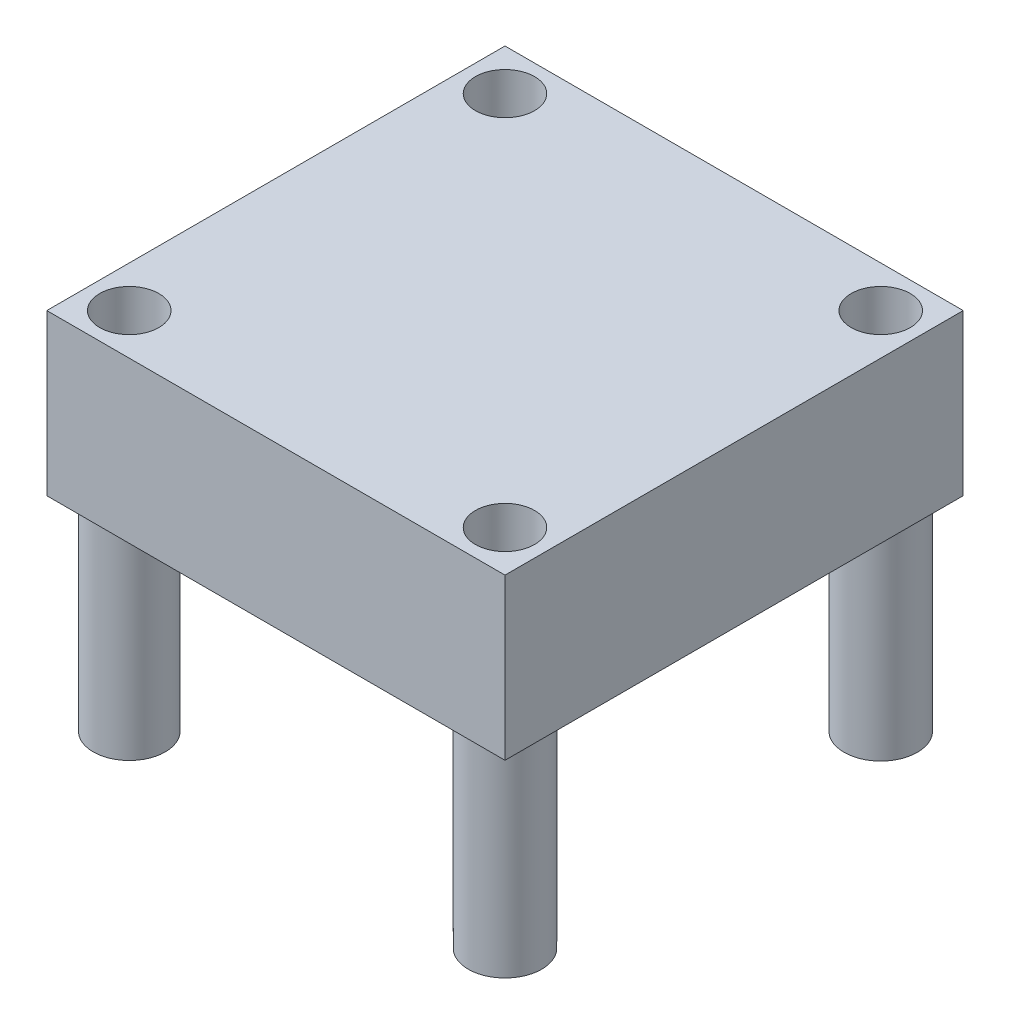
SolidWorks part; units mm, degrees
ref_plane "Front Plane" through (0, 0, 0) normal (0, 0, 1) x (1, 0, 0)
ref_plane "Top Plane" through (0, 0, 0) normal (0, 1, 0) x (1, 0, 0)
ref_plane "Right Plane" through (0, 0, 0) normal (1, 0, 0) x (0, 0, -1)
sketch "Sketch1" plane through (0, 0, 0) normal (0, 1, 0) x (1, 0, 0)
  line L1 (-16.8639, 11.4761) -> (8.5361, 11.4761)
  line L2 (-16.8639, 11.4761) -> (-16.8639, -13.9239)
  line L3 (-16.8639, -13.9239) -> (8.5361, -13.9239)
  line L4 (8.5361, 11.4761) -> (8.5361, -13.9239)
  dimension "D1" = 25.4
  dimension "D2" = 25.4
extrude "Boss-Extrude1" add sketch "Sketch1" along normal blind 8.89
sketch "Sketch2" plane through (0, 0, 0) normal (0, -1, 0) x (1, 0, 0)
  line L0 (-16.8639, -11.4761) -> (-16.8639, 13.9239) construction
  line L1 (-16.8639, 13.9239) -> (8.5361, 13.9239) construction
  line L2 (8.5361, -11.4761) -> (-16.8639, -11.4761) construction
  line L3 (8.5361, 13.9239) -> (8.5361, -11.4761) construction
  circle A0 centre (-14.5779, 11.6379) radius 1.9939
  circle A1 centre (6.2501, 11.6379) radius 2.032
  circle A2 centre (6.2501, -9.1901) radius 2.032
  circle A3 centre (-14.5779, -9.1901) radius 2.032
  dimension "D1" = 3.9878
  dimension "D3" = 2.286
  dimension "D6" = 4.064
  dimension "D7" = 2.286
  dimension "D8" = 2.286
  dimension "D9" = 4.064
  dimension "D11" = 2.286
  dimension "D12" = 4.064
  dimension "D2" = 2.286
  dimension "D4" = 2.286
  dimension "D5" = 2.286
  dimension "D10" = 2.286
extrude "Boss-Extrude2" add sketch "Sketch2" along normal blind 11.303
sketch "Sketch3" plane through (0, -11.303, 0) normal (0, -1, 0) x (1, 0, 0)
  circle A0 centre (-14.5779, 11.6379) radius 1.6383
  circle A1 centre (-14.5779, -9.1901) radius 1.6383
  circle A2 centre (6.2501, -9.1901) radius 1.6383
  circle A3 centre (6.2501, 11.6379) radius 1.6383
  dimension "D1" = 3.2766
  dimension "D2" = 3.2766
  dimension "D3" = 3.2766
  dimension "D4" = 3.2766
extrude "Cut-Extrude1" cut sketch "Sketch3" against normal through all
